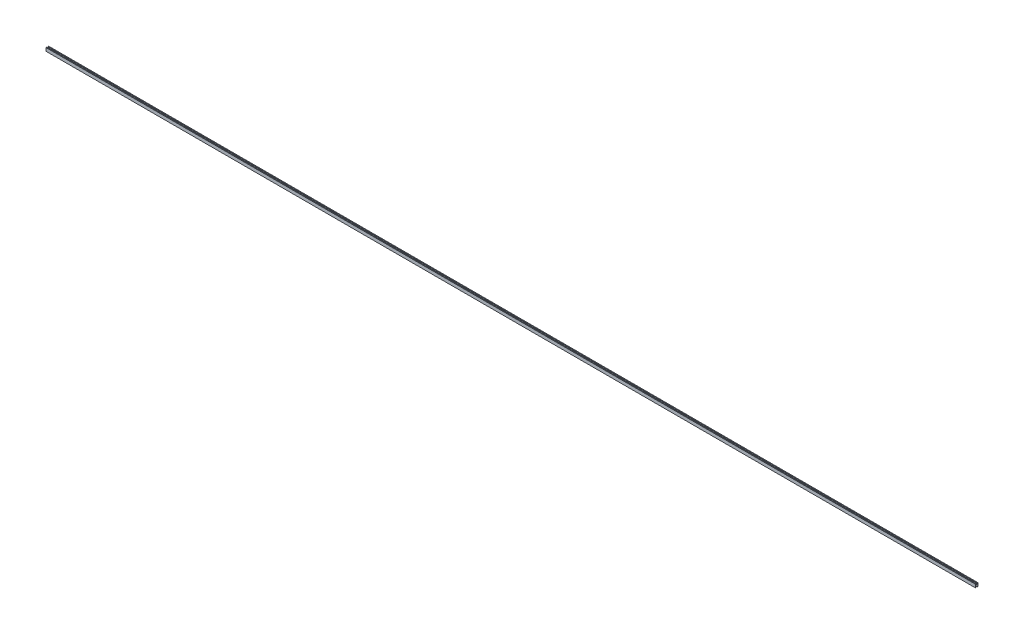
SolidWorks part; units mm, degrees
ref_plane "Front Plane" through (0, 0, 0) normal (0, 0, 1) x (1, 0, 0)
ref_plane "Top Plane" through (0, 0, 0) normal (0, 1, 0) x (1, 0, 0)
ref_plane "Right Plane" through (0, 0, 0) normal (1, 0, 0) x (0, 0, -1)
sketch "Sketch1" plane through (0, 0, 0) normal (1, 0, 0) x (0, 0, -1)
  line L0 (5.08, -15.875) -> (12.7, -15.875)
  line L1 (-12.7, -15.875) -> (-5.08, -15.875)
  line L2 (-12.7, -15.875) -> (-12.7, 15.875)
  line L3 (-12.7, 15.875) -> (-5.08, 15.875)
  line L4 (12.7, -15.875) -> (12.7, 15.875)
  line L5 (-12.7, -15.875) -> (12.7, 15.875) construction
  line L6 (-12.7, 15.875) -> (12.7, -15.875) construction
  line L7 (-5.08, 15.875) -> (-5.08, 6.985)
  line L8 (-5.08, 6.985) -> (5.08, 6.985)
  line L9 (5.08, 6.985) -> (5.08, 15.875)
  line L10 (-12.7, 0) -> (12.7, 0) construction
  line L11 (-5.08, -15.875) -> (-5.08, -6.985)
  line L12 (-5.08, -6.985) -> (5.08, -6.985)
  line L13 (5.08, -6.985) -> (5.08, -15.875)
  line L14 (5.08, 15.875) -> (12.7, 15.875)
  point P0 (0, 0)
  point P17 (0, 0)
extrude "Boss-Extrude1" add sketch "Sketch1" along normal blind 9144 contours L7 L8 L9 L14 L4 L0 L13 L12 L11 L1 L2 L3
